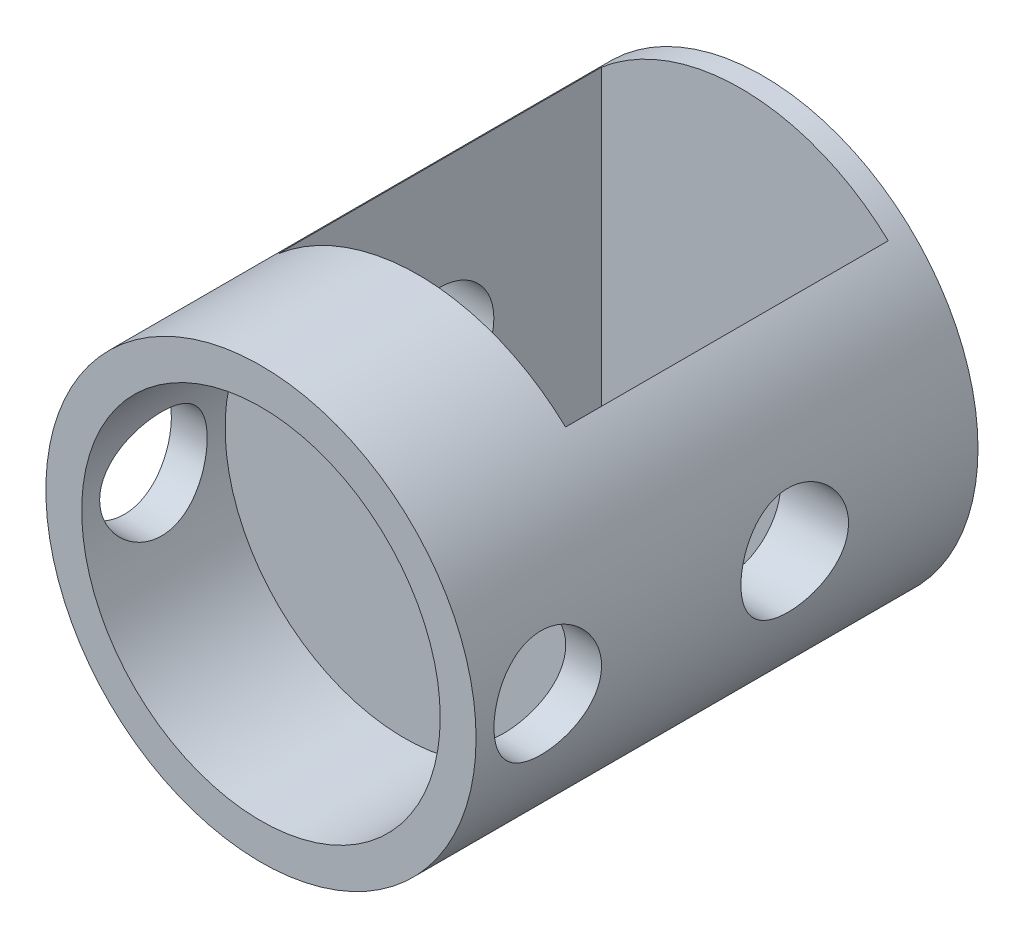
SolidWorks part; units mm, degrees
ref_plane "Front Plane" through (0, 0, 0) normal (0, 0, 1) x (1, 0, 0)
ref_plane "Top Plane" through (0, 0, 0) normal (0, 1, 0) x (1, 0, 0)
ref_plane "Right Plane" through (0, 0, 0) normal (1, 0, 0) x (0, 0, -1)
sketch "Sketch2" plane through (0, 0, 0) normal (0, 0, 1) x (1, 0, 0)
  circle A0 centre (0, 0) radius 6
  dimension "D1" = 12
extrude "Boss-Extrude1" add sketch "Sketch2" along normal blind 14
sketch "Sketch3" plane through (0, 0, 14) normal (0, 0, 1) x (1, 0, 0)
  circle A0 centre (0, 0) radius 5
  dimension "D1" = 10
extrude "Cut-Extrude1" cut sketch "Sketch3" against normal blind 4
sketch "Sketch4" plane through (0, 0, 0) normal (1, 0, 0) x (0, 0, -1)
  line L0 (-14, 0) -> (-10, 0) construction
  line L1 (-14, 6) -> (-14, -6) construction
  circle A0 centre (-12, 0) radius 1.5
  dimension "D2" = 3
  dimension "D1" = 4
extrude "Cut-Extrude2" cut sketch "Sketch4" against normal through all and the other way through all from offset 0
sketch "Sketch7" plane through (0, 0, 0) normal (0, 1, 0) x (1, 0, 0)
  line L0 (-6.1143, -10.2225) -> (6, -10.2225) construction
  line L1 (6, -10.5) -> (6, 0) construction
  line L2 (-6.1143, -10.2225) -> (6.3294, 0) construction
  line L3 (6, 0) -> (-6, 0) construction
  line L5 (-3.8924, -0.6112) -> (4.1076, -0.6112)
  line L6 (-3.8924, -0.6112) -> (-3.8924, -9.6112)
  line L7 (-3.8924, -9.6112) -> (4.1076, -9.6112)
  line L8 (4.1076, -0.6112) -> (4.1076, -9.6112)
  line L9 (-3.8924, -0.6112) -> (4.1076, -9.6112) construction
  line L10 (-3.8924, -9.6112) -> (4.1076, -0.6112) construction
  point P4 (0.1076, -5.1112)
  dimension "D1" = 9
  dimension "D2" = 8
extrude "Cut-Extrude5" cut sketch "Sketch7" against normal through all and the other way through all
sketch "Sketch8" plane through (0, 0, 0) normal (1, 0, 0) x (0, 0, -1)
  line L0 (-9.6112, 4.3735) -> (-0.6112, -4.3735) construction
  line L1 (-0.6112, 4.3735) -> (-9.6112, -4.3735) construction
  circle A0 centre (-5.1112, 0) radius 1.5
  dimension "D1" = 3
extrude "Cut-Extrude6" cut sketch "Sketch8" against normal through all and the other way through all
